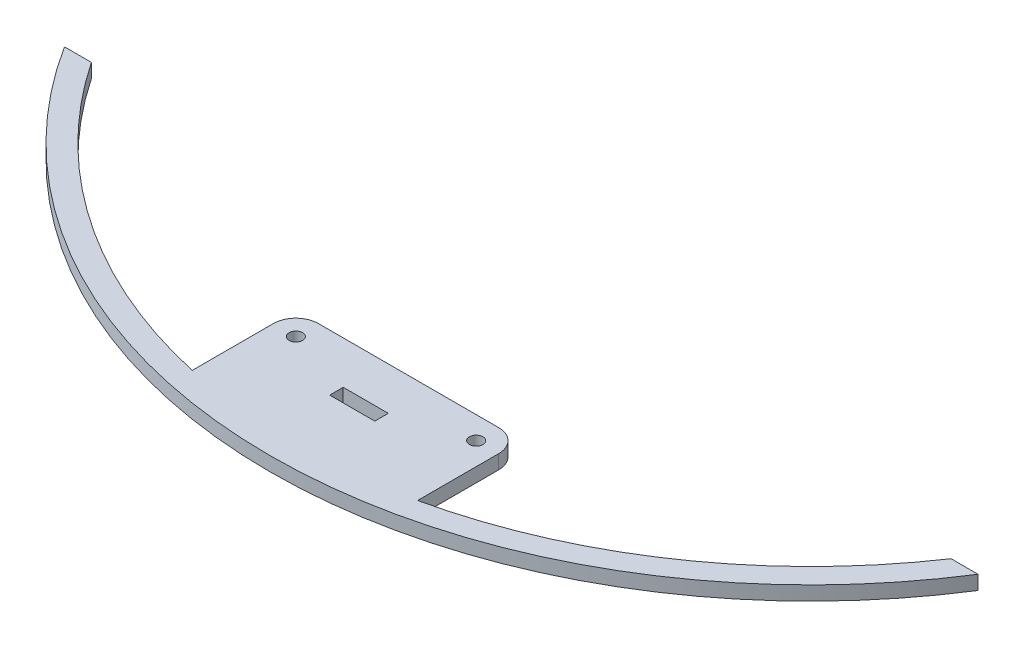
SolidWorks part; units mm, degrees
ref_plane "前视基准面" through (0, 0, 0) normal (0, 0, 1) x (1, 0, 0)
ref_plane "上视基准面" through (0, 0, 0) normal (0, 1, 0) x (1, 0, 0)
ref_plane "右视基准面" through (0, 0, 0) normal (1, 0, 0) x (0, 0, -1)
other "Configuration Table"
sketch "草图1" plane through (0, 0, 0) normal (0, 1, 0) x (1, 0, 0)
  line L0 (0, 0) -> (29.2916, 0) construction
  line L1 (0, 1410) -> (0, 205) construction
  line L2 (-101.3507, 30) -> (-95.3781, 30)
  line L3 (-20, 5) -> (20, 5)
  line L4 (-25, 0) -> (-25, -18)
  line L6 (25, 0) -> (25, -18)
  line L7 (0, 30) -> (0, -27.5318) construction
  line L8 (95.3781, 30) -> (101.3507, 30)
  line L10 (-5, -4.5) -> (5, -4.5)
  line L11 (-5, -4.5) -> (-5, -7.5)
  line L12 (-5, -7.5) -> (5, -7.5)
  line L13 (5, -4.5) -> (5, -7.5)
  line L14 (-5, -4.5) -> (5, -7.5) construction
  line L15 (-5, -7.5) -> (5, -4.5) construction
  arc A2 (20, 5) -> (25, 0) centre (20, 0) cw
  arc A3 (-20, 5) -> (-25, 0) centre (-20, 0) ccw
  arc A4 (-101.3507, 30) -> (101.3507, 30) centre (0, 94.2497) ccw
  arc A5 (25, -18) -> (95.3781, 30) centre (0, 94.2497) ccw
  arc A6 (-95.3781, 30) -> (-25, -18) centre (0, 94.2497) ccw
  circle A7 centre (-20, 0) radius 1.5
  circle A8 centre (20, 0) radius 1.5
  point P9 (0, 5)
  point P17 (25, 5)
  point P20 (-25, 5)
  point P21 (0, 94.2497)
  point P25 (0, -6)
  dimension "D2" = 3
  dimension "D4" = 5
  dimension "D7" = 240
  dimension "D8" = 230
  dimension "D1" = 50
  dimension "D3" = 20
  dimension "D5" = 30
  dimension "D6" = 5
  dimension "D9" = 6
  dimension "D10" = 3
  dimension "D11" = 10
  dimension "D12" = 18
extrude "凸台-拉伸2" add sketch "草图1" along normal blind 3.125
